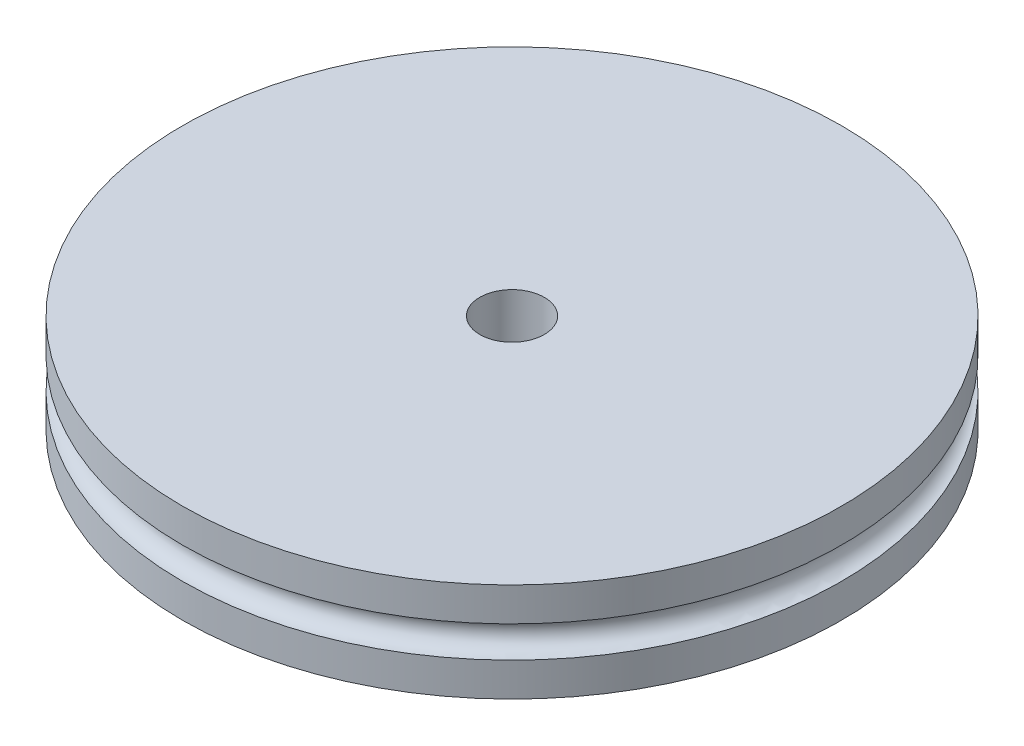
SolidWorks part; units mm, degrees
ref_plane "Front Plane" through (0, 0, 0) normal (0, 0, 1) x (1, 0, 0)
ref_plane "Top Plane" through (0, 0, 0) normal (0, 1, 0) x (1, 0, 0)
ref_plane "Right Plane" through (0, 0, 0) normal (1, 0, 0) x (0, 0, -1)
sketch "Sketch1" plane through (0, 0, 0) normal (0, 1, 0) x (1, 0, 0)
  circle A0 centre (0, 0) radius 33.3375
  circle A1 centre (0, 0) radius 30.1625 construction
  dimension "D1" = 3.175
  dimension "D2" = 60.325
extrude "Boss-Extrude1" add sketch "Sketch1" along normal blind 10
sketch "Sketch2" plane through (0, 0, 0) normal (0, 0, 1) x (1, 0, 0)
  line L0 (0, 10) -> (0, 0) construction
  line L1 (33.3375, 10) -> (-33.3375, 10) construction
  line L2 (33.3375, 0) -> (33.3375, 10) construction
  circle A0 centre (33.3375, 5) radius 1.5875
  dimension "D1" = 3.175
revolve "Cut-Revolve1" cut sketch "Sketch2" angle 360 about L0
hole_wizard "5/16-18 Tapped Hole1" positions "Sketch4" profile "Sketch3" tap size "5/16-18" standard "ANSI Inch" end condition through all
sketch "Sketch4" plane through (0, 10, 0) normal (0, 1, 0) x (1, 0, 0)
  point P0 (0, 0)
sketch "Sketch3" plane through (0, 10, 0) normal (1, 0, 0) x (0, 0, 1)
  line L0 (0, 0) -> (0, 10)
  line L1 (0, 10) -> (3.2639, 10)
  line L2 (3.2639, 10) -> (3.2639, 0)
  line L5 (3.2639, 0) -> (0, 0)
  line L11 (0, -6.35) -> (0, 107.95) construction
  dimension "Thru Tap Drill Dia." = 6.5278
  dimension "Thru Tap Drill Depth" = 10
cosmetic thread "Hole Thread1" parameters "D2"=7.9375
